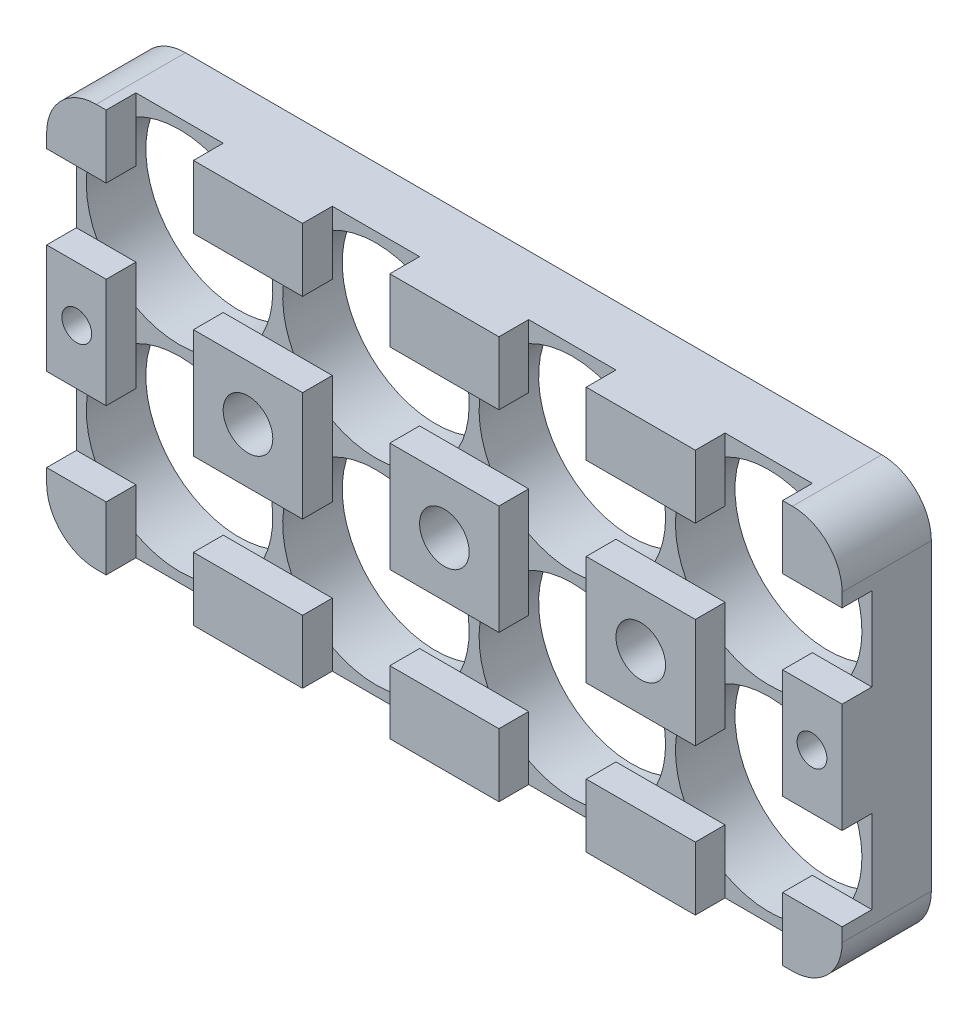
SolidWorks part; units mm, degrees
ref_plane "前视基准面" through (0, 0, 0) normal (0, 0, 1) x (1, 0, 0)
ref_plane "上视基准面" through (0, 0, 0) normal (0, 1, 0) x (1, 0, 0)
ref_plane "右视基准面" through (0, 0, 0) normal (1, 0, 0) x (0, 0, -1)
sketch "草图1" plane through (0, 0, 0) normal (0, 0, 1) x (1, 0, 0)
  line L0 (0, 0) -> (0, 10.4) construction
  line L1 (0, 10.4) -> (-10.4, 10.4) construction
  line L2 (0, -19.8) -> (0, -30.2) construction
  line L3 (0, -30.2) -> (-10.4, -30.2) construction
  line L4 (59.4, 0) -> (59.4, 10.4) construction
  line L5 (59.4, 10.4) -> (69.8, 10.4) construction
  line L6 (59.4, -19.8) -> (69.8, -19.8) construction
  line L7 (69.8, -19.8) -> (69.8, -30.2) construction
  line L8 (-10.4, 10.4) -> (69.8, 10.4)
  line L9 (69.8, 10.4) -> (69.8, -30.2)
  line L10 (69.8, -30.2) -> (-10.4, -30.2)
  line L11 (-10.4, -30.2) -> (-10.4, 10.4)
  line L12 (0, 0) -> (19.8, -19.8) construction
  line L13 (19.8, 0) -> (0, -19.8) construction
  circle A0 centre (0, 0) radius 9.4
  circle A1 centre (19.8, 0) radius 9.4
  circle A2 centre (39.6, 0) radius 9.4
  circle A3 centre (59.4, 0) radius 9.4
  circle A4 centre (0, -19.8) radius 9.4
  circle A5 centre (19.8, -19.8) radius 9.4
  circle A6 centre (39.6, -19.8) radius 9.4
  circle A7 centre (59.4, -19.8) radius 9.4
  circle A8 centre (9.9, -9.9) radius 2.5
  circle A9 centre (29.7, -9.9) radius 2.5
  circle A10 centre (49.5, -9.9) radius 2.5
  dimension "D1" = 4
  dimension "D3" = 3
  dimension "D2" = 2
extrude "凸台-拉伸1" add sketch "草图1" along normal blind 6
sketch "草图2" plane through (0, 0, 6) normal (0, 0, 1) x (1, 0, 0)
  line L1 (-10.4, 10.4) -> (69.8, 10.4)
  line L2 (-10.4, 10.4) -> (-10.4, -30.2)
  line L3 (-10.4, -30.2) -> (69.8, -30.2)
  line L4 (69.8, 10.4) -> (69.8, -30.2)
extrude "凸台-拉伸2" add sketch "草图2" along normal blind 3
sketch "草图3" plane through (0, 0, 9) normal (0, 0, 1) x (1, 0, 0)
  line L0 (-10.4, 10.4) -> (-10.4, 0) construction
  line L1 (-10.4, 10.4) -> (-10.4, -30.2) construction
  line L2 (-10.4, 10.4) -> (-10.4, 4.02) construction
  line L3 (69.8, -30.2) -> (69.8, 10.4) construction
  line L4 (-10.4, 4.02) -> (69.8, 4.02)
  line L5 (-10.4, 4.02) -> (-10.4, -4.38)
  line L6 (-10.4, -4.38) -> (69.8, -4.38)
  line L7 (69.8, 4.02) -> (69.8, -4.38)
  line L8 (-10.4, -9.9) -> (69.8, -9.9) construction
  line L9 (69.8, -9.9) -> (71.0783, -12.0717) construction
  line L10 (-10.4, -15.42) -> (69.8, -15.42)
  line L11 (69.8, -23.82) -> (69.8, -15.42)
  line L12 (-10.4, -23.82) -> (69.8, -23.82)
  line L13 (-10.4, -23.82) -> (-10.4, -15.42)
  line L14 (69.8, -9.9) -> (71.0783, -7.7283) construction
extrude "切除-拉伸1" cut sketch "草图3" against normal blind 3
sketch "草图4" plane through (0, 0, 9) normal (0, 0, 1) x (1, 0, 0)
  line L0 (-10.4, 10.4) -> (-4.4, 10.4) construction
  line L1 (69.8, 10.4) -> (-10.4, 10.4) construction
  line L2 (-10.4, -30.2) -> (69.8, -30.2) construction
  line L3 (-4.4, 10.4) -> (4.4, 10.4)
  line L4 (-4.4, 10.4) -> (-4.4, -30.2)
  line L5 (-4.4, -30.2) -> (4.4, -30.2)
  line L6 (4.4, 10.4) -> (4.4, -30.2)
  line L7 (15.4, 10.4) -> (15.4, -30.2)
  line L8 (15.4, 10.4) -> (24.2, 10.4)
  line L9 (24.2, 10.4) -> (24.2, -30.2)
  line L10 (15.4, -30.2) -> (24.2, -30.2)
  line L11 (35.2, 10.4) -> (35.2, -30.2)
  line L12 (35.2, 10.4) -> (44, 10.4)
  line L13 (44, 10.4) -> (44, -30.2)
  line L14 (35.2, -30.2) -> (44, -30.2)
  line L15 (55, 10.4) -> (55, -30.2)
  line L16 (55, 10.4) -> (63.8, 10.4)
  line L17 (63.8, 10.4) -> (63.8, -30.2)
  line L18 (55, -30.2) -> (63.8, -30.2)
  dimension "D1" = 4
extrude "切除-拉伸2" cut sketch "草图4" against normal blind 3
sketch "草图5" plane through (0, 0, 6) normal (0, 0, -1) x (-1, 0, 0)
  line L0 (-29.7, 10.4) -> (-29.7, -34.5592) construction
  line L1 (-69.8, 10.4) -> (10.4, 10.4) construction
  circle A0 centre (-49.5, -9.9) radius 2.5
  circle A1 centre (-29.7, -9.9) radius 2.5
  circle A2 centre (-9.9, -9.9) radius 2.5
  circle A3 centre (-66.7631, -9.9) radius 1.5
  circle A4 centre (7.3631, -9.9) radius 1.5
  dimension "D1" = 3
extrude "切除-拉伸3" cut sketch "草图5" against normal blind 10 and the other way through all
fillet "圆角3" radius 5 1 edges at (-10.4, -30.2, 4.5)
fillet "圆角8" radius 5 1 edges at (69.8, -30.2, 4.5)
fillet "圆角9" radius 5 1 edges at (69.8, 10.4, 4.5)
fillet "圆角10" radius 5 1 edges at (-10.4, 10.4, 4.5)
